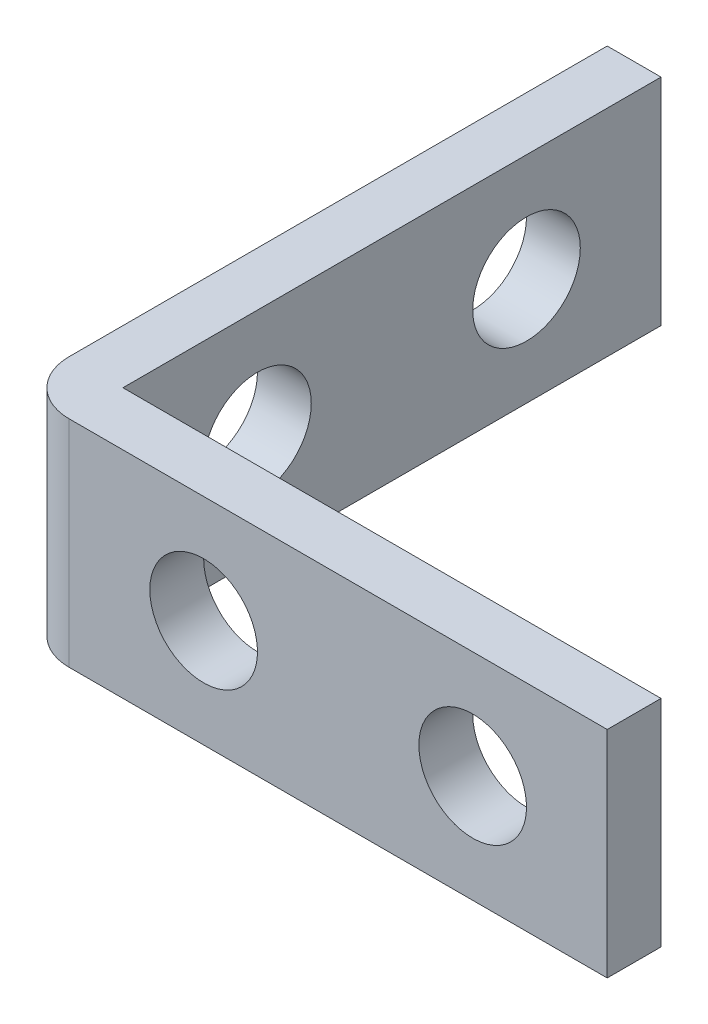
SolidWorks part; units mm, degrees
ref_plane "Front Plane" through (0, 0, 0) normal (0, 0, 1) x (1, 0, 0)
ref_plane "Top Plane" through (0, 0, 0) normal (0, 1, 0) x (1, 0, 0)
ref_plane "Right Plane" through (0, 0, 0) normal (1, 0, 0) x (0, 0, -1)
sketch "Sketch1" plane through (0, 0, 0) normal (0, 1, 0) x (1, 0, 0)
  line L0 (0, 20) -> (0, 0)
  line L1 (0, 0) -> (20, 0)
  line L2 (20, 0) -> (20, -2)
  line L3 (20, -2) -> (-2, -2)
  line L4 (-2, -2) -> (-2, 20)
  line L5 (-2, 20) -> (0, 20)
  dimension "D1" = 20
  dimension "D2" = 20
  dimension "D3" = 2
extrude "Boss-Extrude1" add sketch "Sketch1" along normal blind 8
sketch "Sketch2" plane through (0, 0, 0) normal (0, 0, -1) x (-1, 0, 0)
  line L0 (0, 4) -> (-20, 4) construction
  line L1 (0, 8) -> (0, 0) construction
  line L2 (-20, 8) -> (-20, 0) construction
  circle A0 centre (-15, 4) radius 2
  circle A1 centre (-5, 4) radius 2
  dimension "D1" = 4
  dimension "D2" = 4
  dimension "D3" = 5
  dimension "D4" = 10
sketch "Sketch3" plane through (0, 0, 0) normal (1, 0, 0) x (0, 0, -1)
  line L0 (0, 4) -> (20, 4) construction
  line L1 (20, 8) -> (20, 0) construction
  circle A0 centre (5, 4) radius 2
  circle A1 centre (15, 4) radius 2
  dimension "D1" = 4
  dimension "D2" = 4
  dimension "D3" = 10
  dimension "D4" = 5
extrude "Cut-Extrude1" cut sketch "Sketch2" against normal blind 8
extrude "Cut-Extrude2" cut sketch "Sketch3" against normal blind 8
fillet "Fillet3" radius 2 1 edges at (-2, 4, 2)
